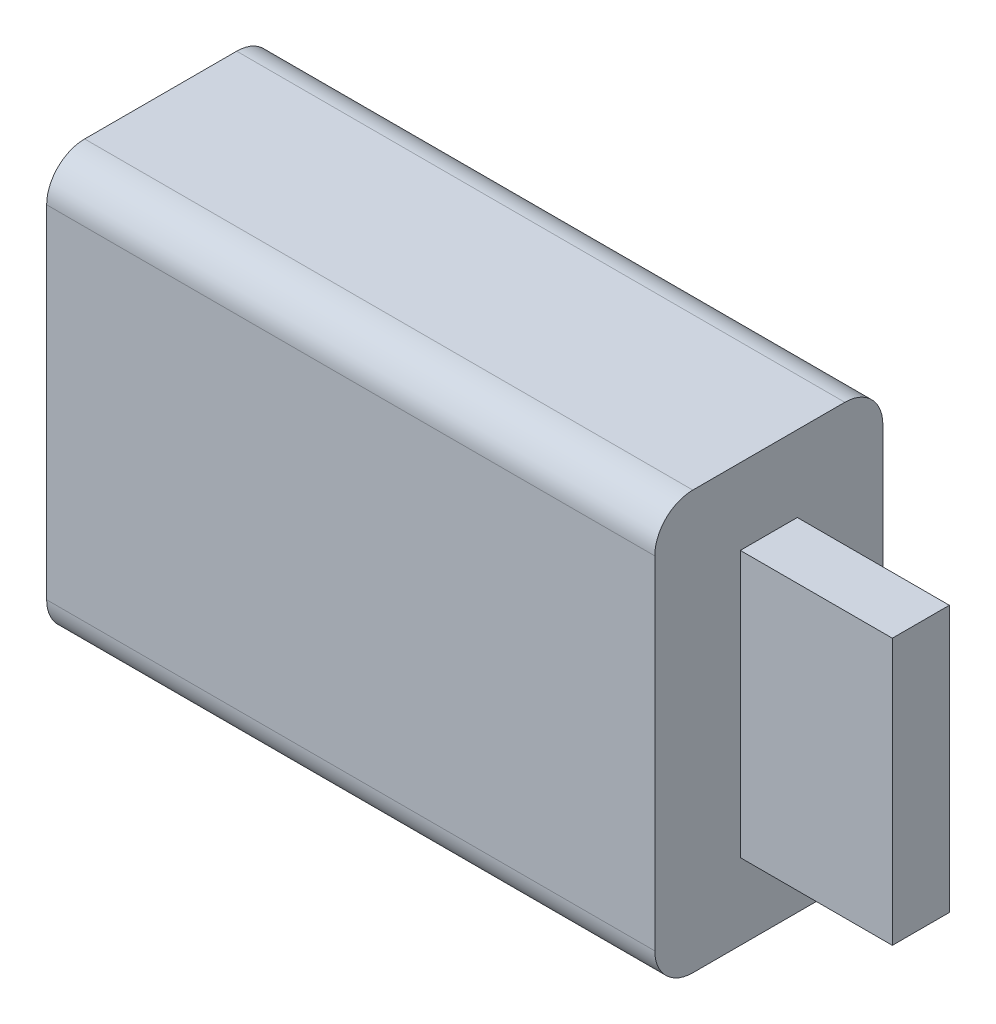
SolidWorks part; units mm, degrees
ref_plane "Přední rovina" through (0, 0, 0) normal (0, 0, 1) x (1, 0, 0)
ref_plane "Horní rovina" through (0, 0, 0) normal (0, 1, 0) x (1, 0, 0)
ref_plane "Pravá rovina" through (0, 0, 0) normal (1, 0, 0) x (0, 0, -1)
sketch "Skica1" plane through (0, 0, 0) normal (0, 0, 1) x (1, 0, 0)
  line L1 (-8, 5.5) -> (8, 5.5)
  line L2 (-8, 5.5) -> (-8, -5.5)
  line L3 (-8, -5.5) -> (8, -5.5)
  line L4 (8, 5.5) -> (8, -5.5)
  line L5 (-8, 5.5) -> (8, -5.5) construction
  line L6 (-8, -5.5) -> (8, 5.5) construction
  point P0 (0, 0)
  dimension "D1" = 11
  dimension "D2" = 16
extrude "Přidat vysunutím1" add sketch "Skica1" along normal blind 6
fillet "Zaoblit1" radius 1 4 edges at (0, -5.5, 0) (0, -5.5, 6) (0, 5.5, 6) (0, 5.5, 0)
sketch "Skica2" plane through (8, 0, 0) normal (1, 0, 0) x (0, 0, -1)
  line L0 (0, 0) -> (-7.8285, 0) construction
  line L1 (-3.75, 3.5) -> (-2.25, 3.5)
  line L2 (-3.75, 3.5) -> (-3.75, -3.5)
  line L3 (-3.75, -3.5) -> (-2.25, -3.5)
  line L4 (-2.25, 3.5) -> (-2.25, -3.5)
  line L5 (-3.75, 3.5) -> (-2.25, -3.5) construction
  line L6 (-3.75, -3.5) -> (-2.25, 3.5) construction
  line L7 (0, -4.5) -> (0, 4.5) construction
  point P0 (-3, 0)
  point P9 (0, 0)
  dimension "D1" = 1.5
  dimension "D2" = 7
  dimension "D3" = 3
extrude "Přidat vysunutím2" add sketch "Skica2" along normal blind 4
